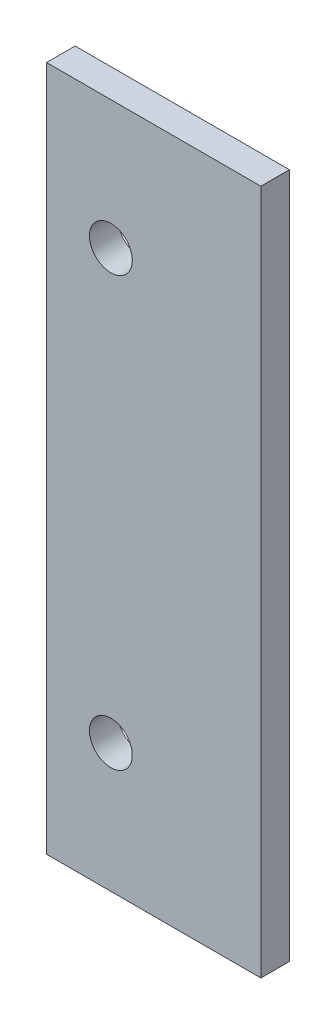
SolidWorks part; units mm, degrees
ref_plane "Plan de face" through (0, 0, 0) normal (0, 0, 1) x (1, 0, 0)
ref_plane "Plan de dessus" through (0, 0, 0) normal (0, 1, 0) x (1, 0, 0)
ref_plane "Plan de droite" through (0, 0, 0) normal (1, 0, 0) x (0, 0, -1)
sketch "Esquisse1" plane through (0, 0, 0) normal (0, 0, 1) x (1, 0, 0)
  line L0 (0, 0) -> (15, 0)
  line L1 (15, 0) -> (15, -48)
  line L2 (15, -48) -> (0, -48)
  line L3 (0, -48) -> (0, 0)
  line L4 (9, 0) -> (9, -48) construction
  line L5 (9, -24) -> (0, -24) construction
  line L6 (4.5, -24) -> (4.5, -9) construction
  circle A0 centre (4.5, -9) radius 1.5
  circle A1 centre (4.5, -39) radius 1.5
  dimension "D1" = 48
  dimension "D3" = 3
  dimension "D4" = 4.5
  dimension "D2" = 15
  dimension "D5" = 15
extrude "Extrusion1" add sketch "Esquisse1" along normal blind 2
